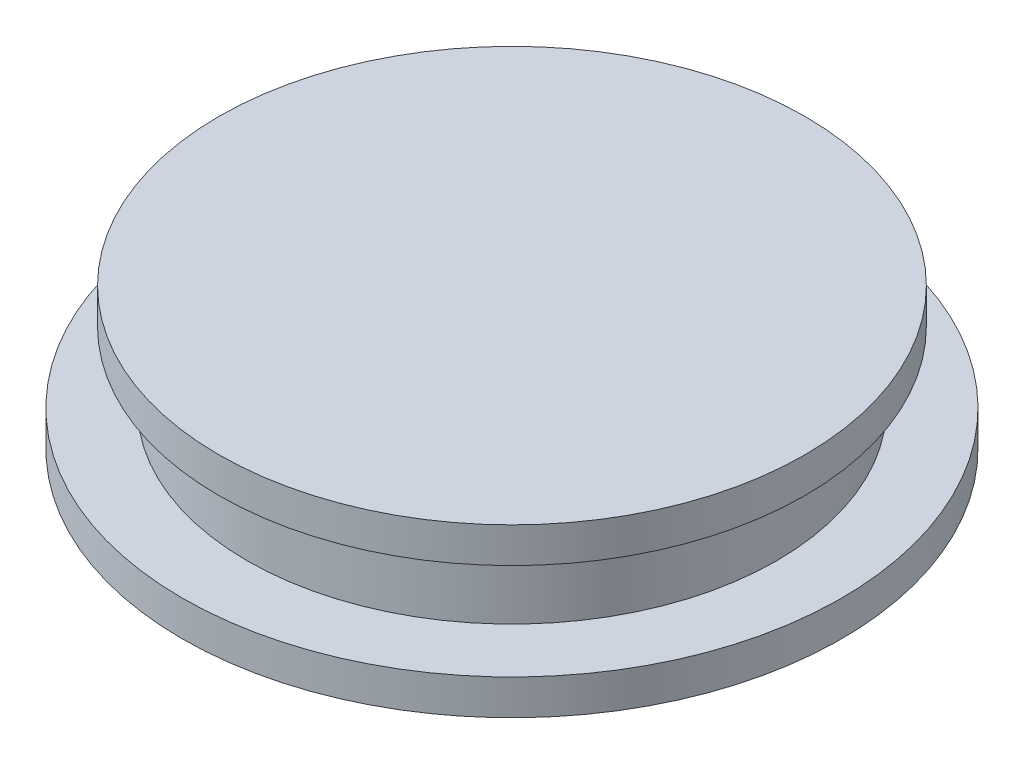
SolidWorks part; units mm, degrees
ref_plane "Front Plane" through (0, 0, 0) normal (0, 0, 1) x (1, 0, 0)
ref_plane "Top Plane" through (0, 0, 0) normal (0, 1, 0) x (1, 0, 0)
ref_plane "Right Plane" through (0, 0, 0) normal (1, 0, 0) x (0, 0, -1)
sketch "Sketch1" plane through (0, 0, 0) normal (0, 1, 0) x (1, 0, 0)
  circle A0 centre (0, 0) radius 18.669
  dimension "D1" = 37.338
extrude "Boss-Extrude1" add sketch "Sketch1" along normal blind 2
sketch "Sketch2" plane through (0, 2, 0) normal (0, 1, 0) x (1, 0, 0)
  circle A0 centre (0, 0) radius 15
  dimension "D1" = 30
extrude "Boss-Extrude2" add sketch "Sketch2" along normal blind 4
sketch "Sketch3" plane through (0, 6, 0) normal (0, 1, 0) x (1, 0, 0)
  circle A0 centre (0, 0) radius 16.6
  dimension "D1" = 33.2
extrude "Boss-Extrude3" add sketch "Sketch3" along normal blind 2
sketch "Sketch4" plane through (0, 0, 0) normal (0, -1, 0) x (-1, 0, 0)
  line L1 (6.5405, 6.5405) -> (-6.5405, 6.5405)
  line L2 (6.5405, 6.5405) -> (6.5405, -6.5405)
  line L3 (6.5405, -6.5405) -> (-6.5405, -6.5405)
  line L4 (-6.5405, 6.5405) -> (-6.5405, -6.5405)
  line L5 (6.5405, 6.5405) -> (-6.5405, -6.5405) construction
  line L6 (6.5405, -6.5405) -> (-6.5405, 6.5405) construction
  point P0 (0, 0)
  dimension "D1" = 13.081
  dimension "D2" = 13.081
extrude "Cut-Extrude1" cut sketch "Sketch4" against normal blind 7
sketch "Sketch5" plane through (0, 0, 0) normal (0, -1, 0) x (1, 0, 0)
  line L1 (-6.5405, 6.5405) -> (6.5405, 6.5405)
  line L2 (-6.5405, 6.5405) -> (-6.5405, -6.5405)
  line L3 (-6.5405, -6.5405) -> (6.5405, -6.5405)
  line L4 (6.5405, 6.5405) -> (6.5405, -6.5405)
  line L5 (-5.461, -5.461) -> (5.461, -5.461)
  line L6 (-5.461, -5.461) -> (-5.461, 5.461)
  line L7 (-5.461, 5.461) -> (5.461, 5.461)
  line L8 (5.461, -5.461) -> (5.461, 5.461)
  line L9 (-5.461, -5.461) -> (5.461, 5.461) construction
  line L10 (-5.461, 5.461) -> (5.461, -5.461) construction
  point P6 (0, 0)
  dimension "D1" = 10.922
  dimension "D2" = 10.922
extrude "Boss-Extrude4" add sketch "Sketch5" against normal blind 1
